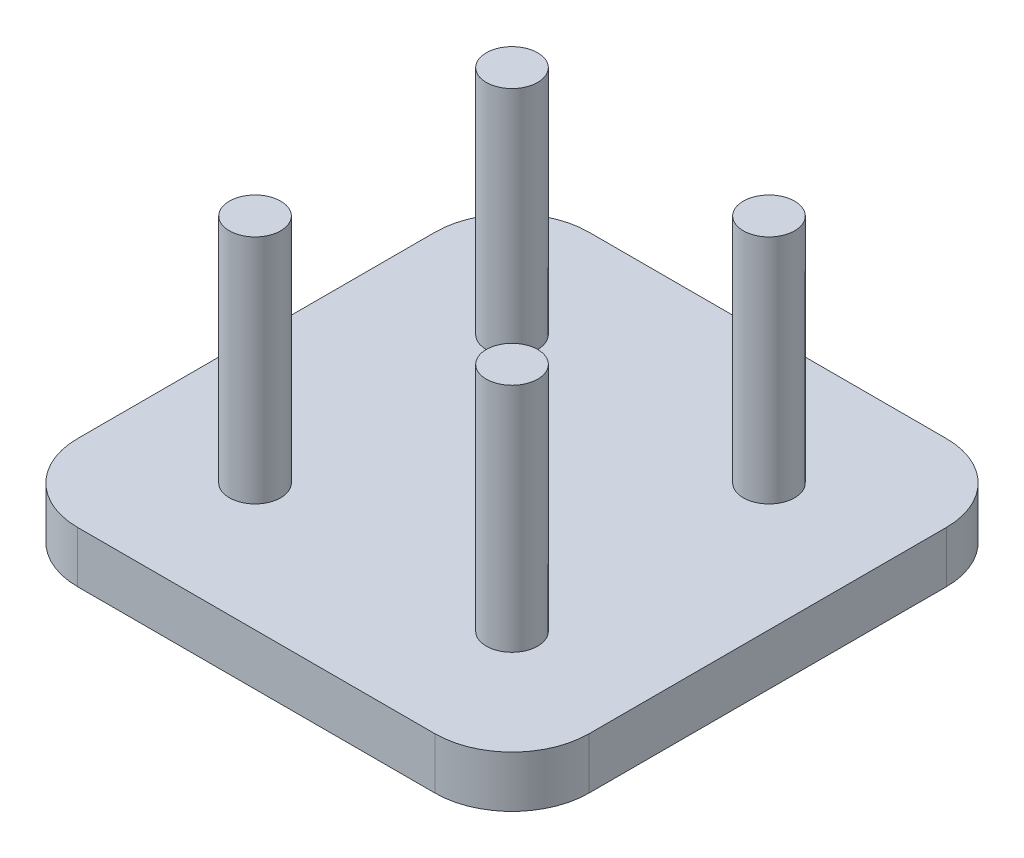
SolidWorks part; units mm, degrees
ref_plane "Front" through (0, 0, 0) normal (0, 0, 1) x (1, 0, 0)
ref_plane "Top" through (0, 0, 0) normal (0, 1, 0) x (1, 0, 0)
ref_plane "Right" through (0, 0, 0) normal (1, 0, 0) x (0, 0, -1)
sketch "Sketch1" plane through (0, 0, 0) normal (0, 1, 0) x (1, 0, 0)
  line L1 (-19.9, -19.9) -> (19.9, -19.9)
  line L2 (-19.9, -19.9) -> (-19.9, 19.9)
  line L3 (-19.9, 19.9) -> (19.9, 19.9)
  line L4 (19.9, -19.9) -> (19.9, 19.9)
  line L5 (0, 19.9) -> (0, -19.9) construction
  line L6 (-19.9, 0) -> (19.9, 0) construction
  point P0 (0, 0)
  dimension "D1" = 39.8
extrude "Boss-Extrude1" add sketch "Sketch1" along normal blind 4
fillet "Fillet1" radius 6 4 edges at (19.9, 2, 19.9) (-19.9, 2, -19.9) (19.9, 2, -19.9) (-19.9, 2, 19.9)
sketch "Sketch2" plane through (0, 4, 0) normal (0, 1, 0) x (1, 0, 0)
  circle A0 centre (-10, 10) radius 2
  circle A1 centre (10, 10) radius 2
  circle A2 centre (10, -10) radius 2
  circle A3 centre (-10, -10) radius 2
  dimension "D1" = 20
  dimension "D2" = 20
  dimension "D3" = 10
  dimension "D4" = 10
  dimension "D5" = 4
extrude "Boss-Extrude2" add sketch "Sketch2" along normal offset from surface (18 mm away) 22 up to face at (0, 0, 0)
